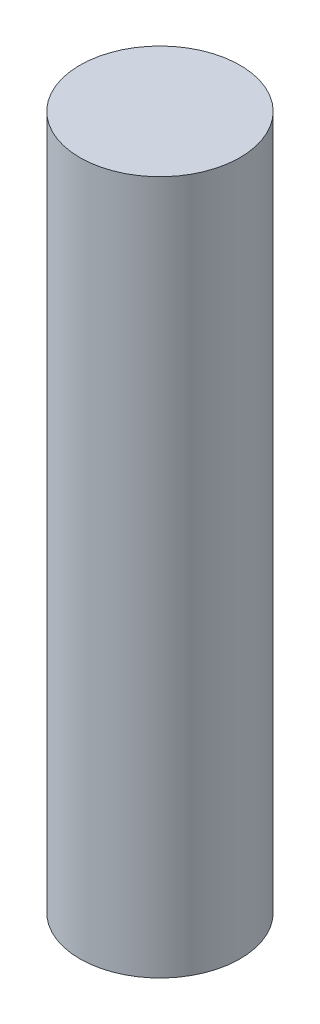
SolidWorks part; units mm, degrees
ref_plane "Front Plane" through (0, 0, 0) normal (0, 0, 1) x (1, 0, 0)
ref_plane "Top Plane" through (0, 0, 0) normal (0, 1, 0) x (1, 0, 0)
ref_plane "Right Plane" through (0, 0, 0) normal (1, 0, 0) x (0, 0, -1)
sketch "Sketch1" plane through (0, 0, 0) normal (0, 1, 0) x (1, 0, 0)
  circle A0 centre (0, 0) radius 3
  dimension "D1" = 6
extrude "Boss-Extrude1" add sketch "Sketch1" along normal blind 26
